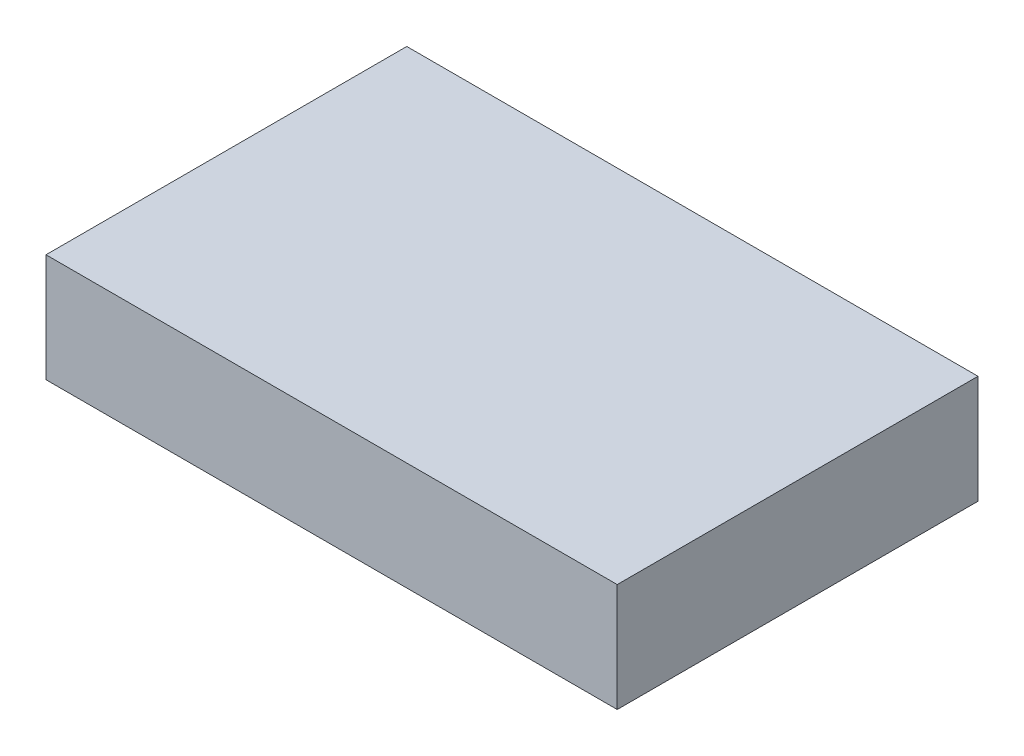
SolidWorks part; units mm, degrees
material "Pin"
ref_plane "Plan de face" through (0, 0, 0) normal (0, 0, 1) x (1, 0, 0)
ref_plane "Plan de dessus" through (0, 0, 0) normal (0, 1, 0) x (1, 0, 0)
ref_plane "Plan de droite" through (0, 0, 0) normal (1, 0, 0) x (0, 0, -1)
sketch "Esquisse1" plane through (0, 0, 0) normal (0, 1, 0) x (1, 0, 0)
  line L0 (-52.1913, -9.9839) -> (-45.9413, -9.9839) construction
  line L1 (-52.1913, 35.0161) -> (42.8087, 35.0161)
  line L2 (-52.1913, 35.0161) -> (-52.1913, -24.9839)
  line L3 (-52.1913, -24.9839) -> (42.8087, -24.9839)
  line L4 (42.8087, 35.0161) -> (42.8087, -24.9839)
  line L5 (-45.9413, -9.9839) -> (36.5587, -9.9839) construction
  line L6 (36.5587, -9.9839) -> (42.8087, -9.9839) construction
  line L7 (-52.1913, 20.0161) -> (-45.9413, 20.0161) construction
  line L8 (-45.9413, 20.0161) -> (36.5587, 20.0161) construction
  line L9 (36.5587, 20.0161) -> (42.8087, 20.0161) construction
  line L10 (-45.9413, 35.0161) -> (-45.9413, 20.0161) construction
  line L11 (-45.9413, 20.0161) -> (-45.9413, -9.9839) construction
  line L12 (-45.9413, -9.9839) -> (-45.9413, -24.9839) construction
  line L13 (36.5587, 35.0161) -> (36.5587, 20.0161) construction
  line L14 (36.5587, 20.0161) -> (36.5587, -9.9839) construction
  line L15 (36.5587, -9.9839) -> (36.5587, -24.9839) construction
  dimension "D1" = 95
  dimension "D2" = 60
  dimension "D4" = 15
  dimension "D5" = 6.25
extrude "Boss.-Extru.1" add sketch "Esquisse1" along normal blind 18
sketch "Esquisse2" plane through (0, 0, 24.9839) normal (0, 0, 1) x (1, 0, 0)
  line L0 (-52.1913, 9) -> (-32.1913, 9) construction
  line L1 (-52.1913, 18) -> (-52.1913, 0) construction
  line L2 (-32.1913, 9) -> (22.8087, 9) construction
  line L3 (22.8087, 9) -> (42.8087, 9) construction
  line L4 (42.8087, 18) -> (42.8087, 0) construction
  dimension "D2" = 20
